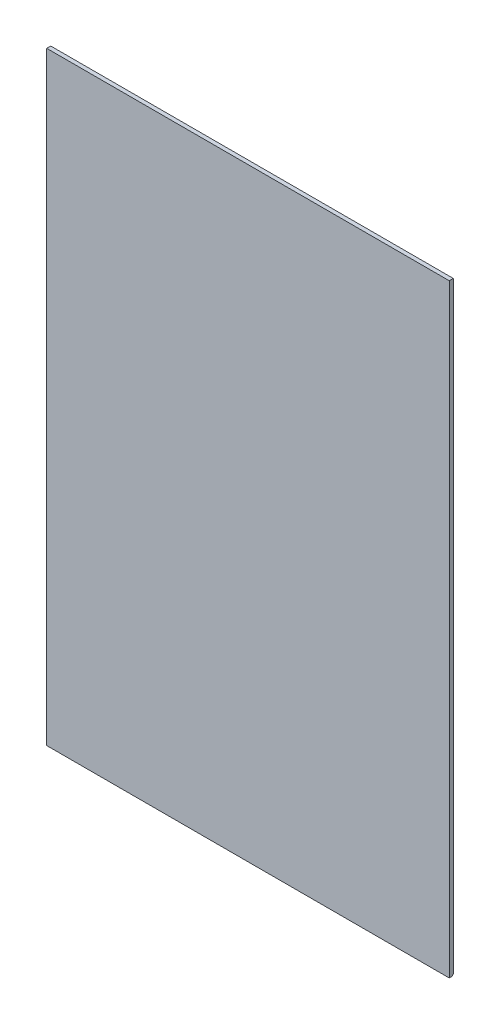
SolidWorks part; units mm, degrees
ref_plane "Plan de face" through (0, 0, 0) normal (0, 0, 1) x (1, 0, 0)
ref_plane "Plan de dessus" through (0, 0, 0) normal (0, 1, 0) x (1, 0, 0)
ref_plane "Plan de droite" through (0, 0, 0) normal (1, 0, 0) x (0, 0, -1)
sketch "Esquisse1" plane through (0, 0, 0) normal (0, 0, 1) x (1, 0, 0)
  line L0 (0, 0) -> (0, 75)
  line L1 (0, 75) -> (50, 75)
  line L2 (50, 75) -> (50, 0)
  line L3 (50, 0) -> (0, 0)
extrude "Boss.-Extru.1" add sketch "Esquisse1" along normal blind 0.5
fillet "Congé1" radius 0.25 1 edges at (25, 0, 0)
